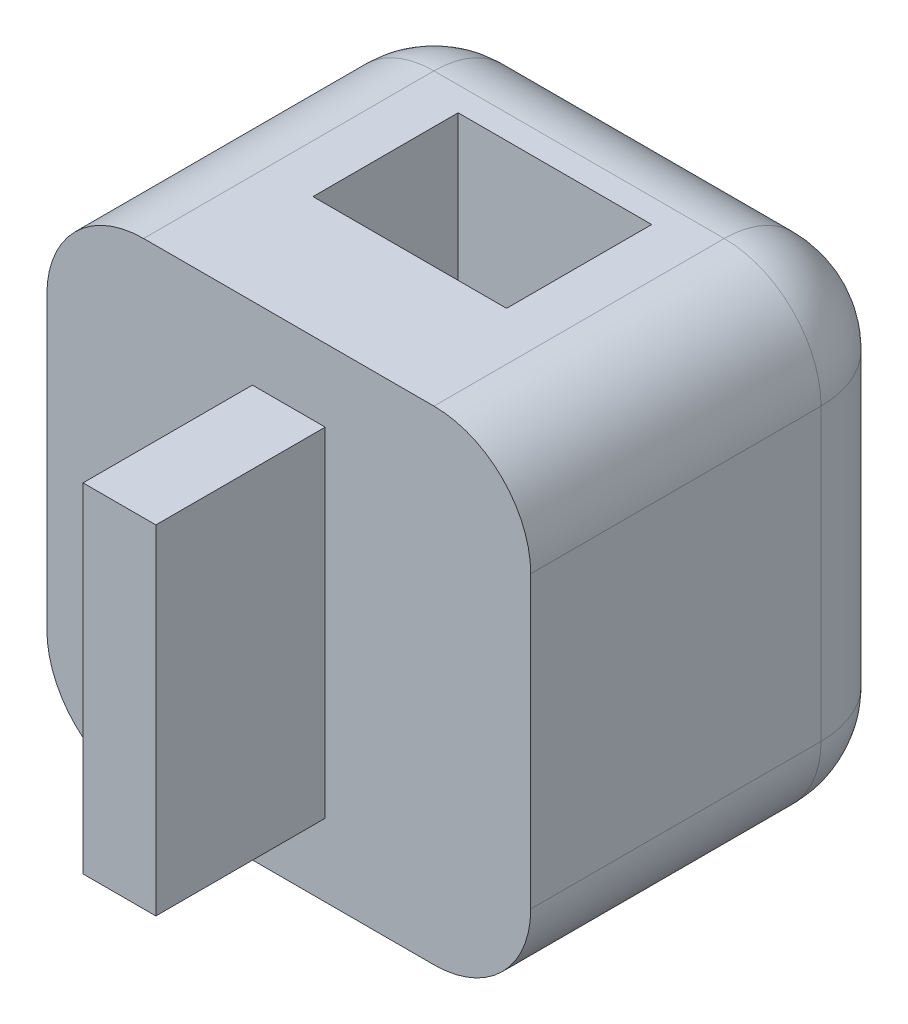
SolidWorks part; units mm, degrees
ref_plane "Front Plane" through (0, 0, 0) normal (0, 0, 1) x (1, 0, 0)
ref_plane "Top Plane" through (0, 0, 0) normal (0, 1, 0) x (1, 0, 0)
ref_plane "Right Plane" through (0, 0, 0) normal (1, 0, 0) x (0, 0, -1)
sketch "Sketch1" plane through (0, 0, 0) normal (0, 0, 1) x (1, 0, 0)
  line L1 (-5, -5) -> (5, -5)
  line L2 (-5, -5) -> (-5, 5)
  line L3 (-5, 5) -> (5, 5)
  line L4 (5, -5) -> (5, 5)
  line L5 (-5, -5) -> (5, 5) construction
  line L6 (-5, 5) -> (5, -5) construction
  point P0 (0, 0)
  dimension "D1" = 10
  dimension "D2" = 10
extrude "Boss-Extrude1" add sketch "Sketch1" along normal blind 8
sketch "Sketch2" plane through (0, -5, 0) normal (0, -1, 0) x (1, 0, 0)
  line L0 (-5, 8) -> (-5, 0) construction
  line L1 (-2, 2.5) -> (2, 2.5)
  line L2 (-2, 2.5) -> (-2, 5.5)
  line L3 (-2, 5.5) -> (2, 5.5)
  line L4 (2, 2.5) -> (2, 5.5)
  line L5 (-2, 2.5) -> (2, 5.5) construction
  line L6 (-2, 5.5) -> (2, 2.5) construction
  point P0 (0, 4)
  point P5 (0, 0)
  point P9 (-5, 4)
  dimension "D1" = 3
  dimension "D2" = 4
extrude "Cut-Extrude1" cut sketch "Sketch2" against normal through all
sketch "Sketch3" plane through (0, 0, 8) normal (0, 0, 1) x (1, 0, 0)
  line L1 (0.7524, -3.5) -> (-0.7524, -3.5)
  line L2 (0.7524, -3.5) -> (0.7524, 3.5)
  line L3 (0.7524, 3.5) -> (-0.7524, 3.5)
  line L4 (-0.7524, -3.5) -> (-0.7524, 3.5)
  line L5 (0.7524, -3.5) -> (-0.7524, 3.5) construction
  line L6 (0.7524, 3.5) -> (-0.7524, -3.5) construction
  point P0 (0, 0)
  dimension "D1" = 1.5049
  dimension "D2" = 7
extrude "Boss-Extrude2" add sketch "Sketch3" along normal blind 3.5
fillet "Fillet1" radius 2 8 edges at (-5, -5, 4) (-5, 5, 4) (5, -5, 4) (5, 5, 4) (0, -5, 0) (0, 5, 0) (-5, 0, 0) (5, 0, 0)
